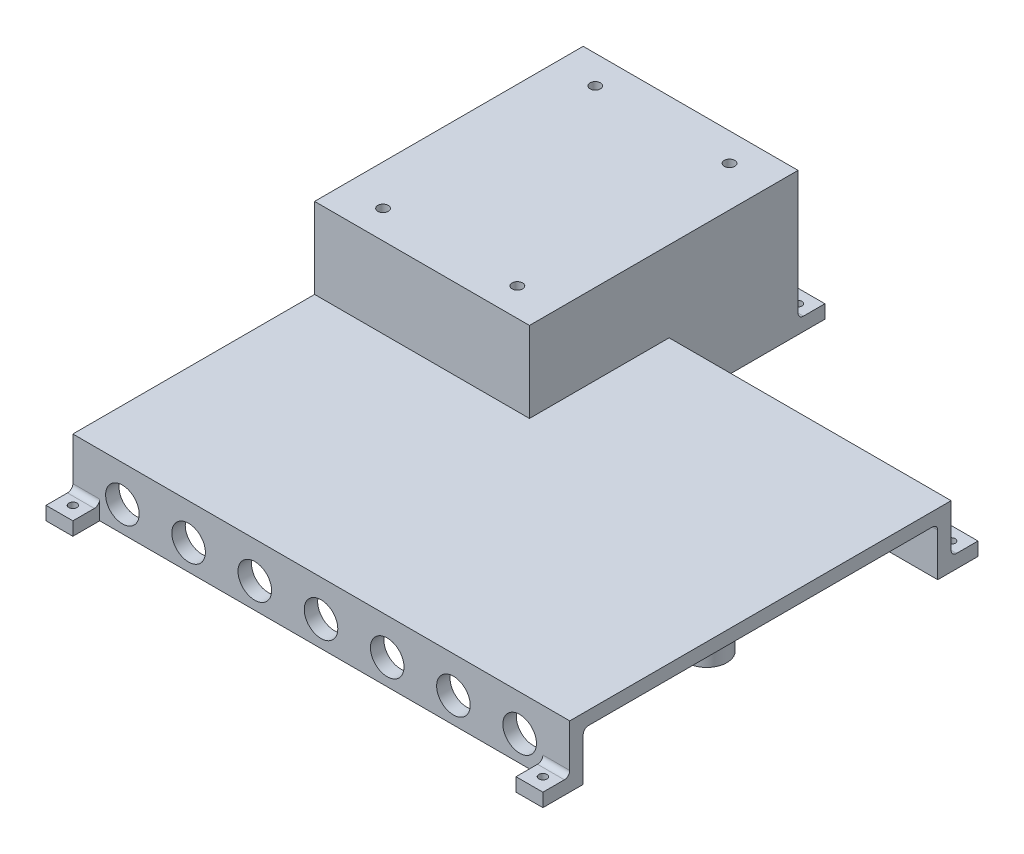
SolidWorks part; units mm, degrees
ref_plane "Front Plane" through (0, 0, 0) normal (0, 0, 1) x (1, 0, 0)
ref_plane "Top Plane" through (0, 0, 0) normal (0, 1, 0) x (1, 0, 0)
ref_plane "Right Plane" through (0, 0, 0) normal (1, 0, 0) x (0, 0, -1)
sketch "Sketch1" plane through (0, 0, 0) normal (0, 1, 0) x (1, 0, 0)
  line L1 (0, 0) -> (185, 0)
  line L2 (0, 0) -> (0, 142)
  line L3 (0, 142) -> (185, 142)
  line L4 (185, 0) -> (185, 142)
  dimension "D1" = 185
  dimension "D2" = 142
extrude "Boss-Extrude1" add sketch "Sketch1" along normal blind 23
sketch "Sketch12" plane through (0, 0, 0) normal (0, 1, 0) x (1, 0, 0)
  line L1 (0, 90) -> (80, 90)
  line L2 (0, 90) -> (0, 190)
  line L3 (0, 190) -> (80, 190)
  line L4 (80, 90) -> (80, 190)
  dimension "D1" = 90
  dimension "D2" = 80
  dimension "D3" = 100
extrude "Boss-Extrude6" add sketch "Sketch12" along normal blind 53
shell "Shell1" thickness 5
sketch "Sketch11" plane through (0, 0, 0) normal (0, 0, 1) x (1, 0, 0)
  line L0 (0, 23) -> (0, 0) construction
  line L1 (0, 0) -> (80, 0) construction
  line L3 (0, 23) -> (185, 23) construction
  circle A6 centre (18.4375, 9.5) radius 6.25
  circle A7 centre (43.0889, 9.5) radius 6.25
  circle A8 centre (67.7402, 9.5) radius 6.25
  circle A9 centre (92.3916, 9.5) radius 6.25
  circle A10 centre (117.0429, 9.5) radius 6.25
  circle A11 centre (141.6943, 9.5) radius 6.25
  circle A12 centre (166.3456, 9.5) radius 6.25
  dimension "D1" = 12.5
  dimension "D6" = 9.5
  dimension "D2" = 18.4375
  dimension "D4" = 24.6514
  dimension "D5" = 13.5
  dimension "D3" = 7
extrude "Cut-Extrude2" cut sketch "Sketch11" against normal blind 6
fillet "Fillet1" radius 2 5 edges at (92.5, 18, -5) (130, 18, -137) (75, 48, -140) (37.5, 48, -95) (37.5, 48, -185)
sketch "Sketch13" plane through (0, 53, 0) normal (0, 1, 0) x (1, 0, 0)
  line L1 (0, 140) -> (80, 140) construction
  line L2 (0, 90) -> (0, 190) construction
  line L3 (80, 90) -> (80, 190) construction
  line L4 (40, 190) -> (40, 90) construction
  line L5 (0, 190) -> (80, 190) construction
  line L6 (0, 90) -> (80, 90) construction
  circle A0 centre (15, 100.5) radius 1.95
  circle A1 centre (15, 179.5) radius 1.95
  circle A2 centre (65, 179.5) radius 1.95
  circle A3 centre (65, 100.5) radius 1.95
  dimension "D1" = 3.9
  dimension "D2" = 79
  dimension "D3" = 50
extrude "Cut-Extrude3" cut sketch "Sketch13" against normal through all
sketch "Sketch15" plane through (0, 0, 0) normal (0, 0, 1) x (1, 0, 0)
  line L1 (0, 0) -> (10, 0)
  line L2 (0, 0) -> (0, 5)
  line L3 (0, 5) -> (10, 5)
  line L4 (10, 0) -> (10, 5)
  line L5 (185, 0) -> (175, 0)
  line L6 (185, 0) -> (185, 5)
  line L7 (185, 5) -> (175, 5)
  line L8 (175, 0) -> (175, 5)
  dimension "D1" = 5
  dimension "D2" = 10
  dimension "D3" = 5
  dimension "D4" = 10
extrude "Boss-Extrude8" add sketch "Sketch15" along normal blind 10
sketch "Sketch16" plane through (0, 0, -190) normal (0, 0, -1) x (-1, 0, 0)
  line L1 (0, 0) -> (-10, 0)
  line L2 (0, 0) -> (0, 5)
  line L3 (0, 5) -> (-10, 5)
  line L4 (-10, 0) -> (-10, 5)
  line L5 (-80, 0) -> (-70, 0)
  line L6 (-80, 0) -> (-80, 5)
  line L7 (-80, 5) -> (-70, 5)
  line L8 (-70, 0) -> (-70, 5)
  dimension "D1" = 10
  dimension "D2" = 5
  dimension "D3" = 10
  dimension "D4" = 5
extrude "Boss-Extrude9" add sketch "Sketch16" along normal blind 10
sketch "Sketch17" plane through (0, 0, -142) normal (0, 0, -1) x (-1, 0, 0)
  line L1 (-185, 0) -> (-175, 0)
  line L2 (-185, 0) -> (-185, 5)
  line L3 (-185, 5) -> (-175, 5)
  line L4 (-175, 0) -> (-175, 5)
  line L5 (-80, 0) -> (-90, 0)
  line L6 (-80, 0) -> (-80, 5)
  line L7 (-80, 5) -> (-90, 5)
  line L8 (-90, 0) -> (-90, 5)
  dimension "D1" = 10
  dimension "D2" = 5
  dimension "D3" = 10
  dimension "D4" = 5
extrude "Boss-Extrude10" add sketch "Sketch17" along normal blind 10
fillet "Fillet2" radius 2 12 edges at (180, 5, 0) (5, 5, 0) (180, 5, -142) (5, 5, -190) (75, 5, -190) (85, 5, -142) (80, 5, -147) (10, 2.5, -190) (70, 2.5, -190) (80, 2.5, -152) (90, 2.5, -142) (175, 2.5, -142)
sketch "Sketch18" plane through (0, 5, 0) normal (0, 1, 0) x (1, 0, 0)
  line L0 (10, 200) -> (10, 192) construction
  line L1 (0, 200) -> (10, 200) construction
  line L3 (80, 200) -> (80, 192) construction
  line L4 (70, 200) -> (80, 200) construction
  line L5 (90, 152) -> (90, 144) construction
  line L6 (82, 152) -> (90, 152) construction
  line L7 (175, 152) -> (175, 144) construction
  line L9 (175, 152) -> (185, 152) construction
  line L11 (185, -10) -> (175, -10) construction
  line L12 (185, -10) -> (185, -2) construction
  line L13 (10, -10) -> (10, -2) construction
  line L14 (10, -10) -> (0, -10) construction
  circle A0 centre (180, 147) radius 1.5
  circle A1 centre (85, 147) radius 1.5
  circle A2 centre (5, -5) radius 1.5
  circle A3 centre (180, -5) radius 1.5
  circle A4 centre (75, 195) radius 1.5
  circle A5 centre (5, 195) radius 1.5
  dimension "D1" = 5
  dimension "D13" = 3
  dimension "D2" = 5
  dimension "D3" = 5
  dimension "D4" = 5
  dimension "D5" = 5
  dimension "D6" = 5
  dimension "D7" = 5
  dimension "D8" = 5
  dimension "D9" = 5
  dimension "D10" = 5
  dimension "D11" = 5
  dimension "D12" = 5
extrude "Cut-Extrude4" cut sketch "Sketch18" against normal blind 10
sketch "Sketch19" plane through (0, 18, 0) normal (0, -1, 0) x (-1, 0, 0)
  line L0 (-185, 7) -> (0, 7) construction
  line L3 (0, 95) -> (0, 7) construction
  line L4 (-185, 7) -> (-185, 135) construction
  circle A0 centre (-165, 71) radius 7.5
  circle A2 centre (-92.5, 71) radius 7.5
  circle A3 centre (-20, 71) radius 7.5
  dimension "D1" = 15
  dimension "D2" = 64
  dimension "D3" = 15
  dimension "D5" = 15
  dimension "D4" = 92.5
  dimension "D6" = 20
  dimension "D7" = 20
extrude "Boss-Extrude11" add sketch "Sketch19" along normal blind 18
fillet "Fillet3" radius 2 3 edges at (20, 18, -78.5) (92.5, 18, -78.5) (165, 18, -78.5)
